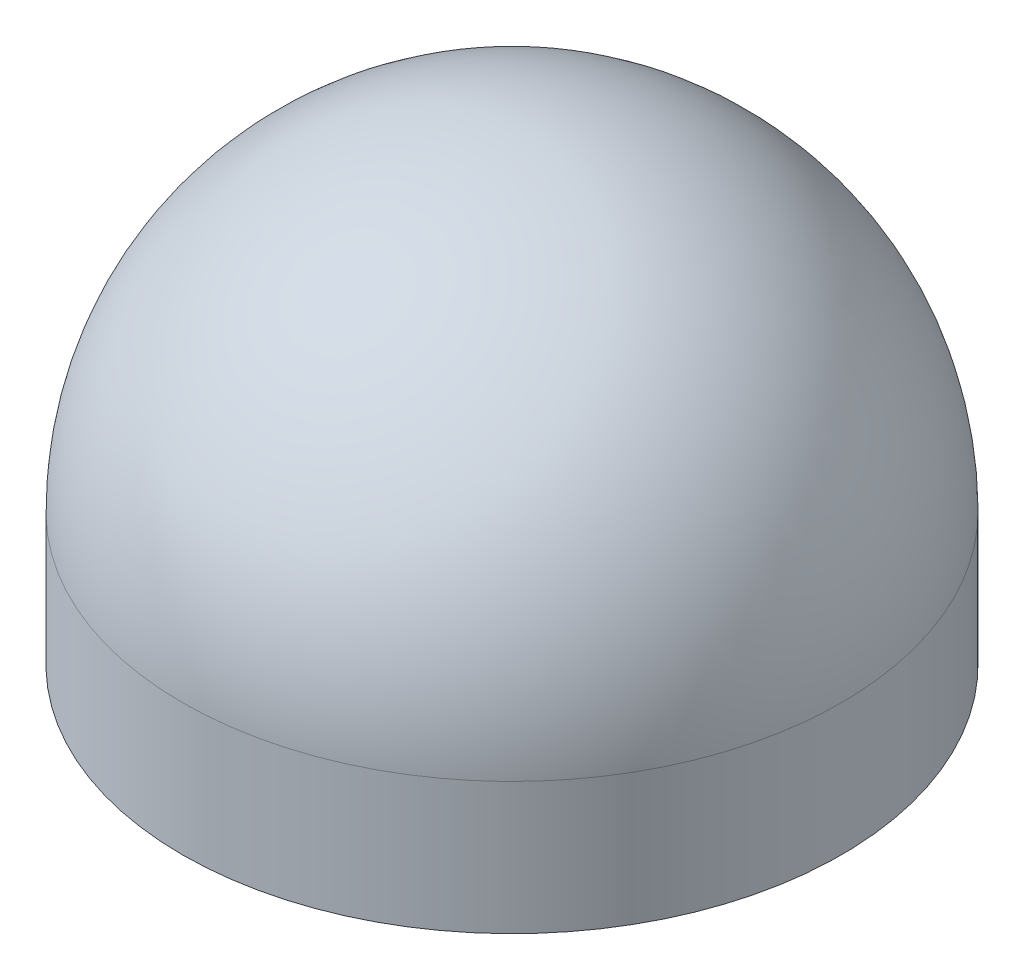
SolidWorks part; units mm, degrees
ref_plane "Front Plane" through (0, 0, 0) normal (0, 0, 1) x (1, 0, 0)
ref_plane "Top Plane" through (0, 0, 0) normal (0, 1, 0) x (1, 0, 0)
ref_plane "Right Plane" through (0, 0, 0) normal (1, 0, 0) x (0, 0, -1)
sketch "Sketch1" plane through (0, 0, 0) normal (0, 1, 0) x (1, 0, 0)
  circle A0 centre (0, 0) radius 5
  dimension "D1" = 10
extrude "Boss-Extrude1" add sketch "Sketch1" along normal blind 7
fillet "Fillet1" radius 5 1 edges at (0, 7, 5)
sketch "Sketch2" plane through (0, 0, 0) normal (0, -1, 0) x (1, 0, 0)
  circle A0 centre (0, 0) radius 1.75
  dimension "D1" = 3.5
extrude "Cut-Extrude1" cut sketch "Sketch2" against normal blind 4
